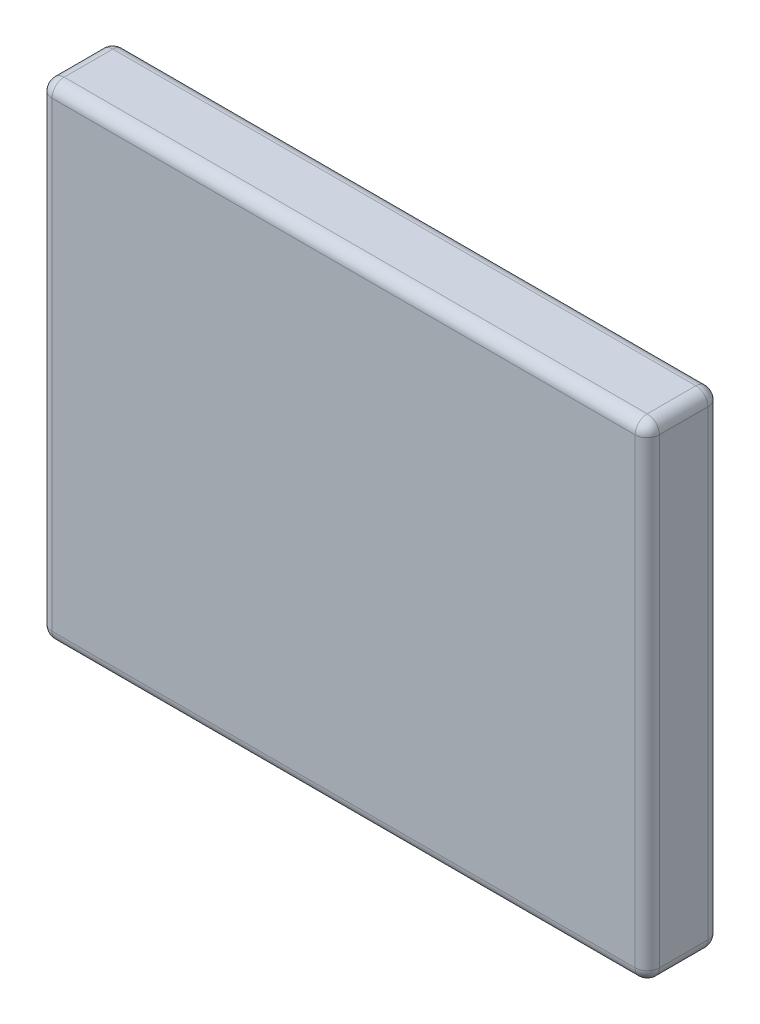
SolidWorks part; units mm, degrees
material "Nylon 6/10"
ref_plane "Piano frontale" through (0, 0, 0) normal (0, 0, 1) x (1, 0, 0)
ref_plane "Piano superiore" through (0, 0, 0) normal (0, 1, 0) x (1, 0, 0)
ref_plane "Piano destro" through (0, 0, 0) normal (1, 0, 0) x (0, 0, -1)
sketch "Schizzo1" plane through (0, 0, 0) normal (0, 0, 1) x (1, 0, 0)
  line L2 (-12.5, 10) -> (12.5, 10)
  line L3 (-12.5, 10) -> (-12.5, -10)
  line L4 (-12.5, -10) -> (12.5, -10)
  line L5 (12.5, 10) -> (12.5, -10)
  line L6 (-12.5, 10) -> (12.5, -10) construction
  line L7 (-12.5, -10) -> (12.5, 10) construction
  line L8 (12.5, 0) -> (-12.5, 0) construction
  point P2 (0, 0)
  dimension "D1" = 25
  dimension "D2" = 20
extrude "Estrusione-Estrusione1" add sketch "Schizzo1" along normal blind 3 contours L3 L4 L5 L2
fillet "Raccordo1" radius 0.5 12 edges at (12.5, 10, 1.5) (-12.5, 0, 0) (0, -10, 0) (12.5, 0, 0) (0, 10, 0) (12.5, 0, 3) (0, -10, 3) (-12.5, 0, 3) (0, 10, 3) (12.5, -10, 1.5) (-12.5, -10, 1.5) (-12.5, 10, 1.5)
